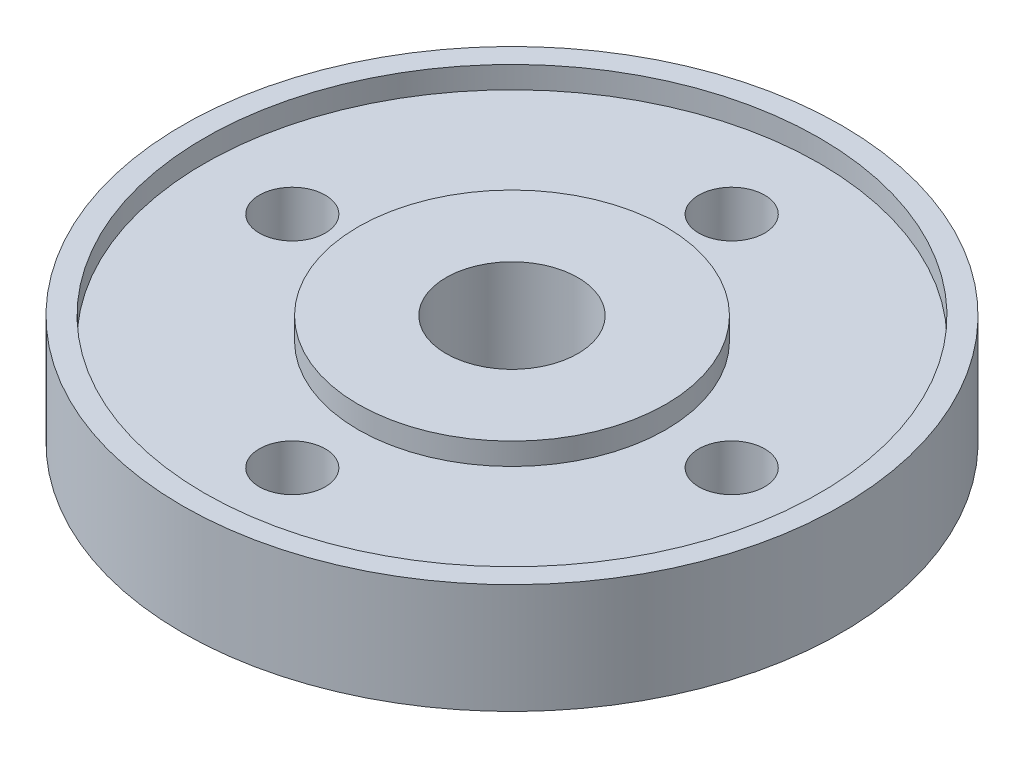
SolidWorks part; units mm, degrees
ref_plane "Front Plane" through (0, 0, 0) normal (0, 0, 1) x (1, 0, 0)
ref_plane "Top Plane" through (0, 0, 0) normal (0, 1, 0) x (1, 0, 0)
ref_plane "Right Plane" through (0, 0, 0) normal (1, 0, 0) x (0, 0, -1)
sketch "Sketch1" plane through (0, 0, 0) normal (0, 1, 0) x (1, 0, 0)
  circle A0 centre (0, 0) radius 15
  circle A1 centre (0, 0) radius 3
  dimension "D1" = 30
  dimension "D2" = 6
extrude "Boss-Extrude1" add sketch "Sketch1" along normal mid plane 5
hole_wizard "Ø3.0mm Dowel Hole1" positions "Sketch5" profile "Sketch4" hole size "Ø3.0" standard "ANSI Metric" end condition up to next
sketch "Sketch5" plane through (0, 2.5, 0) normal (0, 1, 0) x (1, 0, 0)
  line L0 (0, 0) -> (0, 10)
  point P0 (0, 10)
  dimension "D1" = 10
sketch "Sketch4" plane through (0, 2.5, -10) normal (1, 0, 0) x (0, 0, 1)
  line L0 (0, 0) -> (0, 5.001)
  line L1 (0, 5.001) -> (1.5, 5.001)
  line L2 (1.5, 5.001) -> (1.5, 0)
  line L5 (1.5, 0) -> (0, 0)
  line L11 (0, -6.35) -> (0, 107.95) construction
  dimension "Thru Hole Dia." = 3
  dimension "Thru Hole Depth" = 5.001
pattern_circular "CirPattern1" count 4 over 360 about axis through (0, 0, 0) along (0, 1, 0) of "Ø3.0mm Dowel Hole1"
sketch "Sketch6" plane through (0, 2.5, 0) normal (0, 1, 0) x (1, 0, 0)
  circle A0 centre (0, 0) radius 7
  circle A1 centre (0, 0) radius 14
  dimension "D1" = 28
  dimension "D2" = 14
extrude "Cut-Extrude1" cut sketch "Sketch6" against normal blind 1
mirror "Mirror1" about plane through (0, 0, 0) normal (0, 1, 0) of "Cut-Extrude1"
